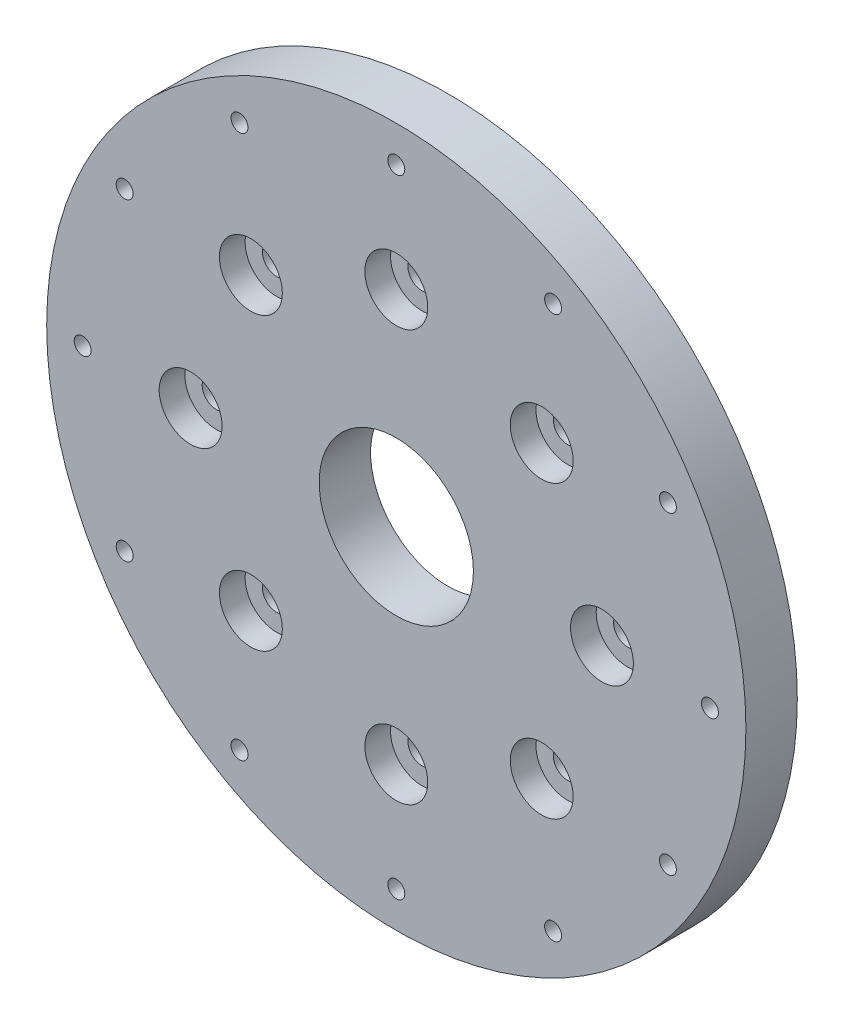
SolidWorks part; units mm, degrees
material "Malleable Cast Iron"
ref_plane "Front Plane" through (0, 0, 0) normal (0, 0, 1) x (1, 0, 0)
ref_plane "Top Plane" through (0, 0, 0) normal (0, 1, 0) x (1, 0, 0)
ref_plane "Right Plane" through (0, 0, 0) normal (1, 0, 0) x (0, 0, -1)
sketch "Sketch1" plane through (0, 0, 0) normal (0, 0, 1) x (1, 0, 0)
  circle A0 centre (0, 0) radius 75
  dimension "D1" = 150
extrude "Boss-Extrude1" add sketch "Sketch1" along normal blind 10
sketch "Sketch3" plane through (0, 0, 10) normal (0, 0, 1) x (1, 0, 0)
  circle A0 centre (0, 0) radius 15
  dimension "D1" = 30
extrude "Cut-Extrude2" cut sketch "Sketch3" against normal blind 10
sketch "Sketch7" plane through (0, 0, 10) normal (0, 0, 1) x (1, 0, 0)
  circle A0 centre (0, 0) radius 55.2 construction
  circle A1 centre (0, 61) radius 2
  dimension "D1" = 110.4
  dimension "D2" = 4
  dimension "D3" = 61
sketch "Sketch8" plane through (0, 0, 0) normal (0, 0, 1) x (1, 0, 0)
  circle A0 centre (0, 0) radius 53
  circle A1 centre (0, 0) radius 55
  dimension "D1" = 106
  dimension "D2" = 110
extrude "Cut-Extrude7" cut sketch "Sketch8" along normal blind 1.3208
hole_wizard "CBORE for M5 Hex Head Bolt1" positions "Sketch9" profile "Sketch10" counterbore size "M5" standard "ISO" end condition through all
sketch "Sketch9" plane through (0, 0, 10) normal (0, 0, 1) x (1, 0, 0)
  line L0 (0, 0) -> (28.2843, 28.2843) construction
  line L3 (0, 0) -> (0, 38.6343) construction
  point P0 (28.2843, 28.2843)
  dimension "D1" = 40
  dimension "D2" = 45
sketch "Sketch10" plane through (28.2843, 28.2843, 10) normal (1, 0, 0) x (0, -1, 0)
  line L0 (0, 0) -> (0, 10)
  line L1 (0, 10) -> (2.75, 10)
  line L3 (2.75, 10) -> (2.75, 3.5)
  line L4 (2.75, 3.5) -> (6.119, 3.5)
  line L5 (6.119, 3.5) -> (6.119, 0)
  line L7 (6.119, 0) -> (0, 0)
  line L11 (0, -6.35) -> (0, 107.95) construction
  dimension "Thru Hole Dia." = 5.5
  dimension "Thru Hole Depth" = 10
  dimension "C'Bore Dia." = 12.238
  dimension "C'Bore Depth" = 3.5
sketch "Sketch11" plane through (0, 0, 10) normal (0, 0, 1) x (1, 0, 0)
  circle A0 centre (0, 0) radius 68
  circle A1 centre (0, 0) radius 75
  dimension "D1" = 136
extrude "Cut-Extrude8" cut sketch "Sketch11" against normal blind 10
sketch "Sketch12" plane through (0, 0, 10) normal (0, 0, 1) x (1, 0, 0)
  circle A0 centre (28.2843, 28.2843) radius 6.119
extrude "Cut-Extrude9" cut sketch "Sketch12" against normal blind 5
pattern_circular "CirPattern2" count 8 over 360 about axis through (0, 0, 0) along (0, 0, 1) of "CBORE for M5 Hex Head Bolt1", "Cut-Extrude9"
hole_wizard "M4 Tapped Hole1" positions "Sketch13" profile "Sketch14" tap size "M4" standard "ISO" end condition through all
sketch "Sketch13" plane through (0, 0, 10) normal (0, 0, 1) x (1, 0, 0)
  point P0 (0, 61)
sketch "Sketch14" plane through (0, 61, 10) normal (1, 0, 0) x (0, -1, 0)
  line L0 (0, 0) -> (0, 10)
  line L1 (0, 10) -> (1.65, 10)
  line L2 (1.65, 10) -> (1.65, 0)
  line L5 (1.65, 0) -> (0, 0)
  line L11 (0, -6.35) -> (0, 107.95) construction
  dimension "Thru Tap Drill Dia." = 3.3
  dimension "Thru Tap Drill Depth" = 10
cosmetic thread "Hole Thread1" parameters "D2"=4
pattern_circular "CirPattern3" count 12 over 360 about axis through (0, 0, 0) along (0, 0, 1) of "M4 Tapped Hole1"
